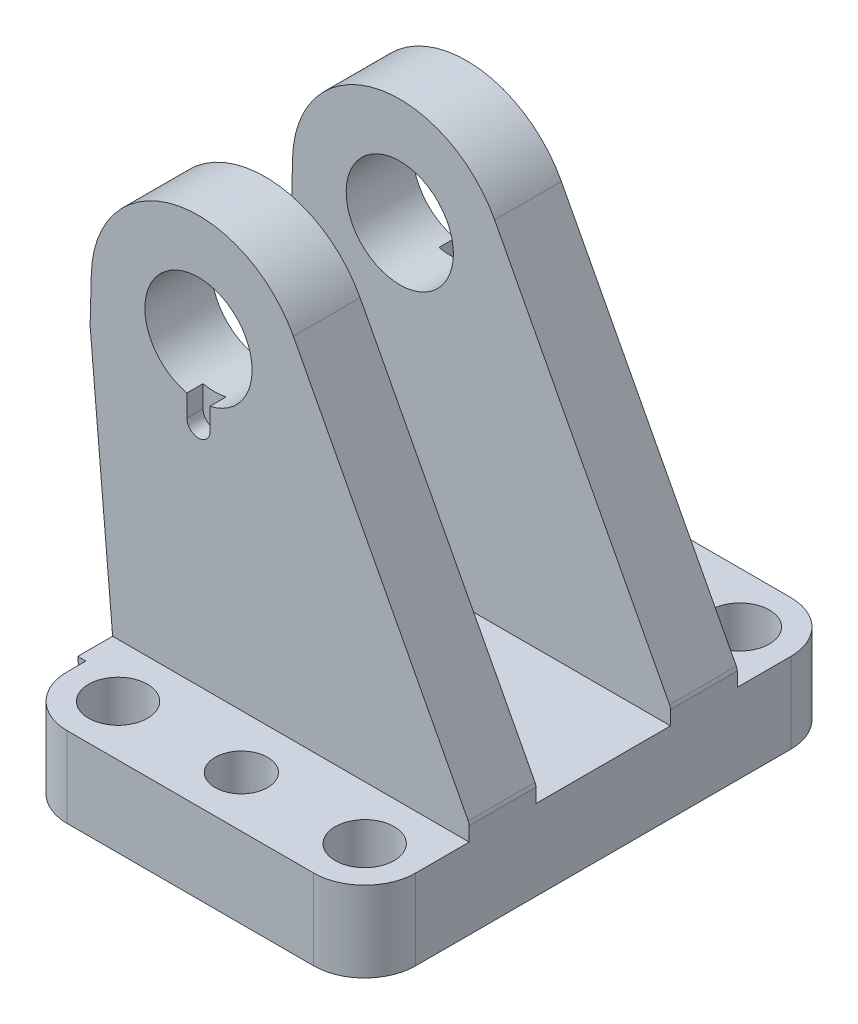
SolidWorks part; units mm, degrees
ref_plane "Front Plane" through (0, 0, 0) normal (0, 0, 1) x (1, 0, 0)
ref_plane "Top Plane" through (0, 0, 0) normal (0, 1, 0) x (1, 0, 0)
ref_plane "Right Plane" through (0, 0, 0) normal (1, 0, 0) x (0, 0, -1)
ref_plane "Plane1" through (0, 0, 0) normal (0, 1, 0) x (1, 0, 0)
sketch "Sketch1" plane through (0, 0, 0) normal (0, 1, 0) x (1, 0, 0)
  line L0 (-23, -44.5) -> (23, -44.5)
  line L1 (32.5, -35) -> (32.5, 35)
  line L2 (23, 44.5) -> (-23, 44.5)
  line L3 (-32.5, 35) -> (-32.5, -35)
  arc A0 (-32.5, -35) -> (-23, -44.5) centre (-23, -35) ccw
  arc A1 (23, -44.5) -> (32.5, -35) centre (23, -35) ccw
  arc A2 (32.5, 35) -> (23, 44.5) centre (23, 35) ccw
  arc A3 (-23, 44.5) -> (-32.5, 35) centre (-23, 35) ccw
  circle A4 centre (23, 35) radius 5.5
  circle A5 centre (23, -35) radius 5.5
  circle A6 centre (0, 35) radius 4.9
  circle A7 centre (0, -35) radius 4.9
  circle A8 centre (-23, 35) radius 5.5
  circle A9 centre (-23, -35) radius 5.5
extrude "Boss-Extrude1" add sketch "Sketch1" along normal blind 15
ref_plane "Plane2" through (0, 0, 0) normal (0, 0, 1) x (1, 0, 0)
sketch "Sketch2" plane through (0, 0, 0) normal (0, 0, 1) x (1, 0, 0)
  line L0 (-34.0123, 15) -> (-32.7, 0)
  line L1 (-32.7, 0) -> (-27.7, 0)
  line L2 (-27.7, 0) -> (-27.7, 15)
  line L3 (-27.7, 15) -> (-34.0123, 15)
extrude "Boss-Extrude2" add sketch "Sketch2" against normal blind 31.5 and the other way blind 31.5
ref_plane "Plane3" through (0, 0, 25) normal (0, 0, 1) x (1, 0, 0)
sketch "Sketch3" plane through (0, 0, 25) normal (0, 0, 1) x (1, 0, 0)
  line L0 (-38.2153, 63.0401) -> (-32.7, 0)
  line L1 (-32.7, 0) -> (32.5, 0)
  line L2 (32.5, 0) -> (32.5, 17.6293)
  line L3 (32.3273, 18.328) -> (-0.3021, 80.3159)
  line L4 (-37.9931, 71.5235) -> (-38.2153, 63.0401)
  arc A0 (32.5, 17.6293) -> (32.3273, 18.328) centre (31, 17.6293) ccw
  arc A1 (-0.3021, 80.3159) -> (-37.9931, 71.5235) centre (-18, 71) ccw
  circle A2 centre (-18, 71) radius 10
extrude "Boss-Extrude3" add sketch "Sketch3" against normal blind 12.45
ref_plane "Plane4" through (0, 0, -25) normal (0, 0, 1) x (1, 0, 0)
sketch "Sketch4" plane through (0, 0, -25) normal (0, 0, 1) x (1, 0, 0)
  line L0 (-38.2153, 63.0401) -> (-32.7, 0)
  line L1 (-32.7, 0) -> (32.5, 0)
  line L2 (32.5, 0) -> (32.5, 17.6293)
  line L3 (32.3273, 18.328) -> (-0.3021, 80.3159)
  line L4 (-37.9931, 71.5235) -> (-38.2153, 63.0401)
  arc A0 (32.5, 17.6293) -> (32.3273, 18.328) centre (31, 17.6293) ccw
  arc A1 (-0.3021, 80.3159) -> (-37.9931, 71.5235) centre (-18, 71) ccw
  circle A2 centre (-18, 71) radius 10
extrude "Boss-Extrude4" add sketch "Sketch4" along normal blind 12.45
ref_plane "Plane5" through (0, 0, 25) normal (0, 0, 1) x (1, 0, 0)
sketch "Sketch5" plane through (0, 0, 25) normal (0, 0, 1) x (1, 0, 0)
  line L0 (-15.85, 57.15) -> (-15.85, 71)
  line L1 (-15.85, 71) -> (-20.15, 71)
  line L2 (-20.15, 71) -> (-20.15, 57.15)
  arc A0 (-20.15, 57.15) -> (-15.85, 57.15) centre (-18, 57.15) ccw
extrude "Cut-Extrude1" cut sketch "Sketch5" against normal blind 3 and the other way blind 3
ref_plane "Plane6" through (0, 0, -25) normal (0, 0, 1) x (1, 0, 0)
sketch "Sketch6" plane through (0, 0, -25) normal (0, 0, 1) x (1, 0, 0)
  line L0 (-15.85, 57.15) -> (-15.85, 71)
  line L1 (-15.85, 71) -> (-20.15, 71)
  line L2 (-20.15, 71) -> (-20.15, 57.15)
  arc A0 (-20.15, 57.15) -> (-15.85, 57.15) centre (-18, 57.15) ccw
extrude "Cut-Extrude2" cut sketch "Sketch6" against normal blind 3 and the other way blind 3
